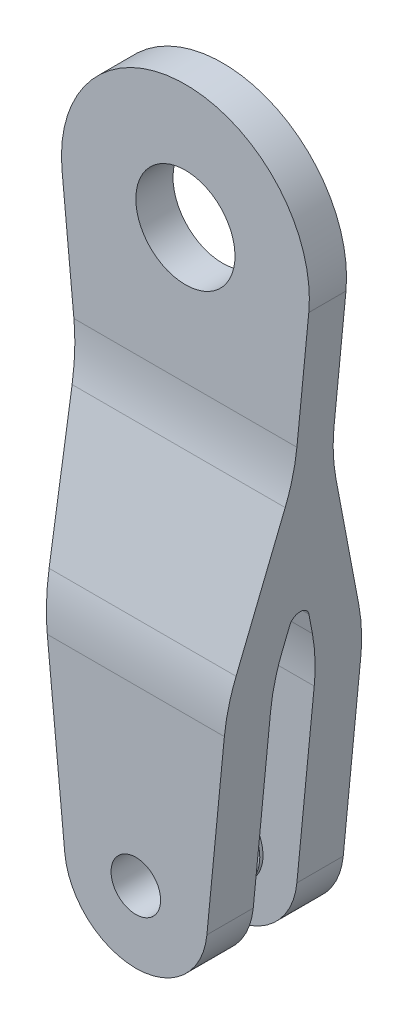
SolidWorks part; units mm, degrees
material "ABS PC"
ref_plane "Front Plane" through (0, 0, 0) normal (0, 0, 1) x (1, 0, 0)
ref_plane "Top Plane" through (0, 0, 0) normal (0, 1, 0) x (1, 0, 0)
ref_plane "Right Plane" through (0, 0, 0) normal (1, 0, 0) x (0, 0, -1)
sketch "Sketch1" plane through (0, 0, 0) normal (0, 0, 1) x (1, 0, 0)
  line L0 (-15.8011, 68.3202) -> (-9.1014, -0.8811)
  line L1 (9.1014, -0.8811) -> (15.8011, 68.3202)
  circle A0 centre (0, 0) radius 3.175
  circle A1 centre (0, 69.85) radius 6.35
  arc A2 (-9.1014, -0.8811) -> (9.1014, -0.8811) centre (0, 0) ccw
  arc A3 (15.8011, 68.3202) -> (-15.8011, 68.3202) centre (0, 69.85) ccw
  point P11 (0, 0)
  point P12 (0, 0)
  dimension "D2" = 6.35
  dimension "D3" = 12.7
  dimension "D4" = 9.144
  dimension "D5" = 9.525
  dimension "D1" = 69.85
extrude "Boss-Extrude1" add sketch "Sketch1" along normal mid plane 17.4625
sketch "Sketch2" plane through (0, -0.4047, 0) normal (1, 0, 0) x (0, 0, -1)
  line L0 (8.7312, 86.1297) -> (-8.7312, 86.1297) construction
  line L1 (8.7312, 86.1297) -> (-8.7312, 86.1297)
  line L2 (-8.7312, -8.7393) -> (8.7312, -8.7393) construction
  line L3 (-8.7312, -8.7393) -> (8.7312, -8.7393)
  line L4 (8.7312, -0.4765) -> (8.7312, 68.7249) construction
  line L5 (-8.7312, -0.4765) -> (-8.7312, 68.7249) construction
  line L6 (8.7312, -0.4765) -> (8.7312, 68.7249)
  line L7 (-8.7312, -0.4765) -> (-8.7312, 68.7249)
  line L8 (8.7312, 68.7249) -> (8.7312, 86.1297)
  line L9 (-8.7312, 68.7249) -> (-8.7312, 86.1297)
  line L10 (-2.794, -8.7393) -> (-2.794, 25.8047)
  line L11 (-2.794, 25.8047) -> (0, 36.232)
  line L12 (0, 36.232) -> (2.794, 25.8047)
  line L13 (2.794, 25.8047) -> (2.794, -8.7393)
  line L14 (-2.3812, 86.1297) -> (-2.3812, 49.6749)
  line L15 (-2.3812, 49.6749) -> (-8.7312, 25.9764)
  line L16 (2.3813, 86.1297) -> (2.3813, 49.6749)
  line L17 (2.3813, 49.6749) -> (8.7312, 25.9764)
  point P20 (0, 0)
  point P21 (-2.6752, 56.2685)
  point P22 (0, 0)
  point P23 (0, 21.1379)
  dimension "D1" = 4.7625
  dimension "D2" = 5.588
  dimension "D3" = 25.4
  dimension "D4" = 5.9372
  dimension "D5" = 15
  dimension "D6" = 19.05
extrude "Cut-Extrude1" cut sketch "Sketch2" against normal through all both and the other way through all
sketch "Sketch3" plane through (0, 0, 8.7312) normal (0, 0, 1) x (1, 0, 0)
  circle A0 centre (0, 0) radius 4.7625
  circle A1 centre (0, 0) radius 3.175 construction
  circle A2 centre (0, 0) radius 3.175
  dimension "D1" = 9.525
extrude "Boss-Extrude2" add sketch "Sketch3" against normal blind 6.35
mirror "Mirror1" about plane through (0, 0, 0) normal (0, 0, 1) of "Boss-Extrude2"
fillet "Fillet1" radius 25.4 6 edges at (0, 25.4, -2.794) (0, 25.4, 2.794) (0, 49.2702, -2.3813) (0, 25.5717, -8.7313) (0, 25.5717, 8.7312) (0, 49.2702, 2.3812)
fillet "Fillet2" radius 1.27 1 edges at (0, 35.8273, 0)
